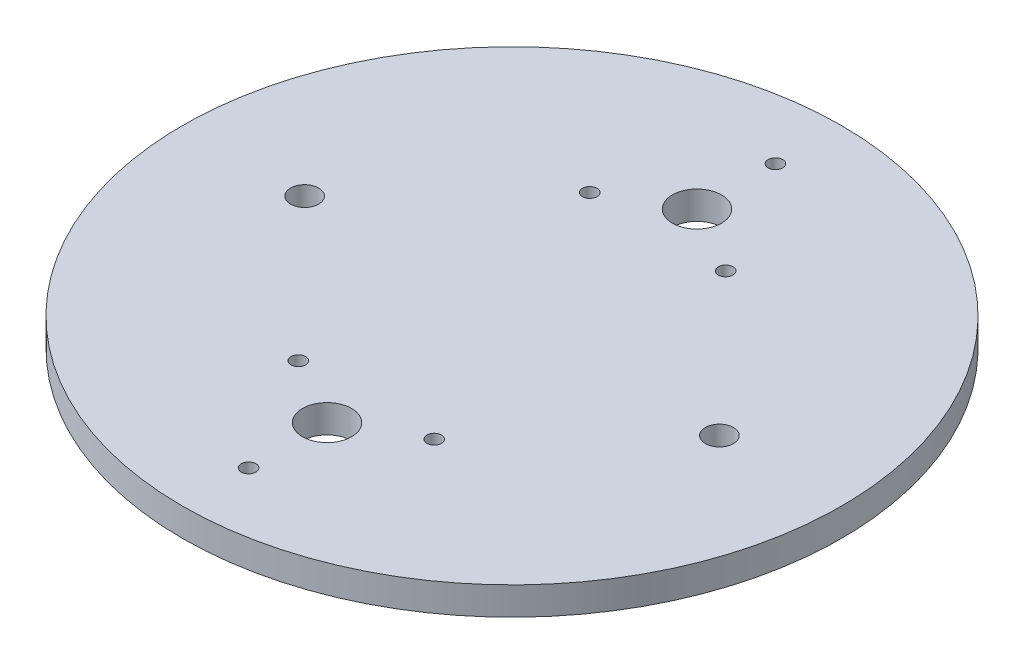
SolidWorks part; units mm, degrees
material "ABS PC"
ref_plane "前视基准面" through (0, 0, 0) normal (0, 0, 1) x (1, 0, 0)
ref_plane "上视基准面" through (0, 0, 0) normal (0, 1, 0) x (1, 0, 0)
ref_plane "右视基准面" through (0, 0, 0) normal (1, 0, 0) x (0, 0, -1)
sketch "Sketch1" plane through (0, 0, 0) normal (0, 1, 0) x (1, 0, 0)
  circle A0 centre (0, 0) radius 74.676
  dimension "D1" = 149.352
extrude "Boss-Extrude1" add sketch "Sketch1" along normal blind 6.35
sketch "Sketch2" plane through (0, 6.35, 0) normal (0, 1, 0) x (1, 0, 0)
  line L1 (-66.782, 0) -> (66.782, 0) construction
  circle A0 centre (15.3979, 33.02) radius 1.651
  circle A1 centre (0, 41.91) radius 21.4376 construction
  circle A2 centre (0, 41.91) radius 5.5626
  circle A3 centre (0, 59.69) radius 1.651
  circle A4 centre (-15.3979, 33.02) radius 1.651
  circle A5 centre (0, -59.69) radius 1.651
  circle A6 centre (-15.3979, -33.02) radius 1.651
  circle A7 centre (0, -41.91) radius 5.5626
  circle A8 centre (15.3979, -33.02) radius 1.651
  point P14 (0, 47.371)
  point P16 (0.2016, 36.7982)
  point P24 (0, 41.91)
  dimension "D1" = 42.8752
  dimension "D2" = 11.1252
  dimension "D4" = 3.302
  dimension "D3" = 17.78
  dimension "D6" = 83.82
  dimension "D7" = 41.91
  dimension "D5" = 3
extrude "CO2Ejec_Flange_Holes" cut sketch "Sketch2" against normal up to surface (6.35 mm away) up to face at (0, 0, 74.676)
sketch "Sketch3" plane through (0, 6.35, 0) normal (0, 1, 0) x (1, 0, 0)
  line L0 (-74.676, 0) -> (74.676, 0) construction
  line L1 (0, 74.676) -> (0, -74.676) construction
  circle A1 centre (-46.99, 0) radius 3.175
  circle A3 centre (46.99, 0) radius 3.175
  dimension "D1" = 6.35
  dimension "D2" = 93.98
extrude "1/4 Holes" cut sketch "Sketch3" against normal up to surface (6.35 mm away) up to face at (0, 0, 47.4726)
